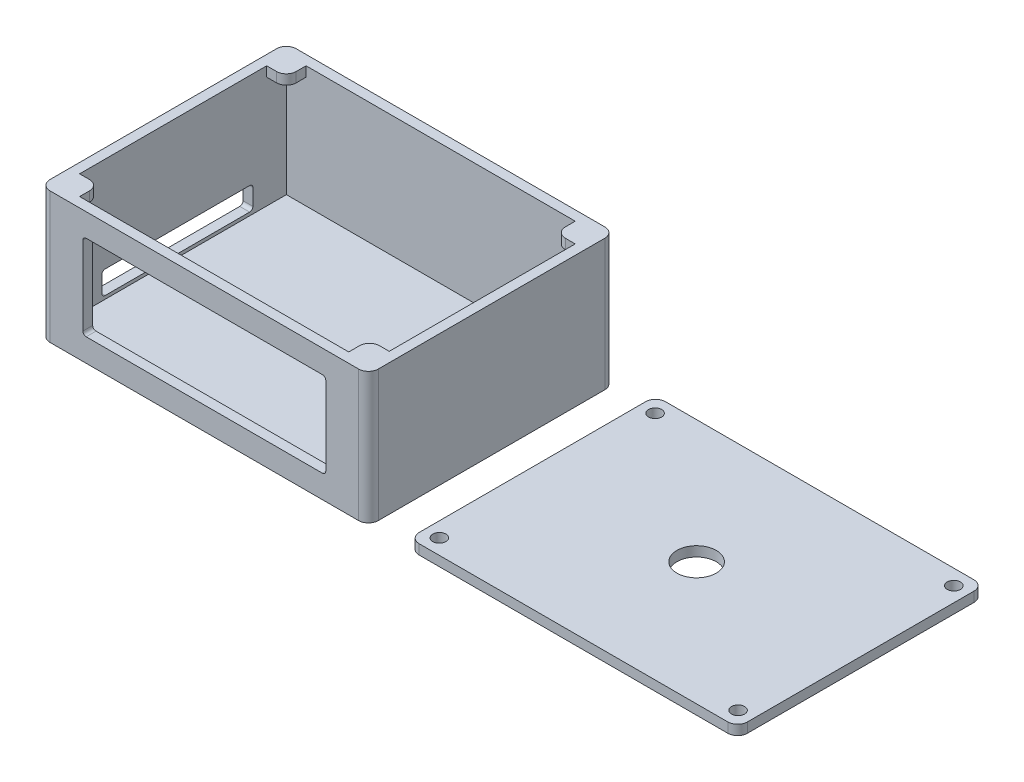
SolidWorks part; units mm, degrees
ref_plane "Ön Düzlem" through (0, 0, 0) normal (0, 0, 1) x (1, 0, 0)
ref_plane "Üst Düzlem" through (0, 0, 0) normal (0, 1, 0) x (1, 0, 0)
ref_plane "Sağ Düzlem" through (0, 0, 0) normal (1, 0, 0) x (0, 0, -1)
sketch "Çizim2" plane through (0, 0, 0) normal (0, 1, 0) x (1, 0, 0)
  line L1 (-45.5172, 36.2069) -> (54.4828, 36.2069)
  line L2 (-45.5172, 36.2069) -> (-45.5172, -38.7931)
  line L3 (-45.5172, -38.7931) -> (54.4828, -38.7931)
  line L4 (54.4828, 36.2069) -> (54.4828, -38.7931)
  dimension "D1" = 100
  dimension "D2" = 75
extrude "Yükseklik-Ekstrüzyon1" add sketch "Çizim2" along normal blind 40
sketch "Çizim4" plane through (0, 40, 0) normal (0, 1, 0) x (1, 0, 0)
  line L0 (4.4828, 36.2069) -> (4.4828, 33.2069)
  line L1 (54.4828, 36.2069) -> (-45.5172, 36.2069) construction
  line L2 (4.4828, -38.7931) -> (4.4828, -35.7931)
  line L3 (-45.5172, -38.7931) -> (54.4828, -38.7931) construction
  line L4 (54.4828, -1.2931) -> (51.4828, -1.2931)
  line L5 (54.4828, -38.7931) -> (54.4828, 36.2069) construction
  line L6 (-45.5172, -1.2931) -> (-42.5172, -1.2931)
  line L7 (-45.5172, 36.2069) -> (-45.5172, -38.7931) construction
  line L9 (-42.5172, -35.7931) -> (51.4828, -35.7931)
  line L10 (51.4828, -35.7931) -> (51.4828, 33.2069)
  line L11 (51.4828, 33.2069) -> (-42.5172, 33.2069)
  line L12 (-42.5172, 33.2069) -> (-42.5172, -35.7931)
extrude "Kes-Ekstrüzyon1" cut sketch "Çizim4" against normal blind 37 contours L12 L9 L10 L11
sketch "Çizim6" plane through (0, 0, 0) normal (0, 0, 1) x (1, 0, 0)
  line L0 (4.4828, 40) -> (4.4828, 0)
  line L1 (-45.5172, 40) -> (54.4828, 40) construction
  line L2 (-45.5172, 0) -> (54.4828, 0) construction
  line L3 (-45.5172, 20) -> (54.4828, 20)
  line L4 (-45.5172, 40) -> (-45.5172, 0) construction
  line L5 (54.4828, 40) -> (54.4828, 0) construction
  line L6 (4.4828, 20) -> (4.4828, 7)
  line L8 (41.4828, 7) -> (41.4828, 33)
  line L9 (41.4828, 33) -> (-32.5172, 33)
  line L10 (-32.5172, 33) -> (-32.5172, 7)
  line L11 (-32.5172, 7) -> (41.4828, 7)
  dimension "D1" = 74
  dimension "D2" = 26
extrude "Kes-Ekstrüzyon2" cut sketch "Çizim6" along normal blind 218 contours L11 L8 L9 L10
sketch "Çizim7" plane through (-45.5172, 0, 0) normal (-1, 0, 0) x (0, 0, 1)
  line L0 (0, 0) -> (0, 4)
  line L2 (23, 4) -> (23, 11)
  line L3 (23, 11) -> (-23, 11)
  line L4 (-23, 11) -> (-23, 4)
  line L5 (-23, 4) -> (23, 4)
extrude "Kes-Ekstrüzyon3" cut sketch "Çizim7" against normal blind 30 contours L4 L5 L2 L3
fillet "Radyus1" radius 3 4 edges at (-45.5172, 20, -36.2069) (54.4828, 20, -36.2069) (54.4828, 20, 38.7931) (-45.5172, 20, 38.7931)
sketch "Çizim9" plane through (0, 40, 0) normal (0, 1, 0) x (1, 0, 0)
  line L0 (-42.5172, 33.2069) -> (-36.5172, 33.2069)
  line L2 (51.4828, 33.2069) -> (-42.5172, 33.2069) construction
  line L3 (-36.5172, 33.2069) -> (-36.5172, 27.2069)
  line L4 (-36.5172, 27.2069) -> (-42.5172, 27.2069)
  line L5 (-42.5172, 33.2069) -> (-42.5172, -35.7931) construction
  line L6 (-42.5172, 27.2069) -> (-42.5172, 33.2069)
extrude "Yükseklik-Ekstrüzyon2" add sketch "Çizim9" against normal blind 3
fillet "Radyus2" radius 3 1 edges at (-36.5172, 38.5, -27.2069)
sketch "Çizim11" plane through (0, 40, 0) normal (0, 1, 0) x (1, 0, 0)
  line L0 (51.4828, 33.2069) -> (45.4828, 33.2069)
  line L1 (51.4828, 33.2069) -> (-42.5172, 33.2069) construction
  line L2 (45.4828, 33.2069) -> (45.4828, 27.2069)
  line L3 (45.4828, 27.2069) -> (51.4828, 27.2069)
  line L4 (51.4828, -35.7931) -> (51.4828, 33.2069) construction
  line L5 (51.4828, 27.2069) -> (51.4828, 33.2069)
extrude "Yükseklik-Ekstrüzyon3" add sketch "Çizim11" against normal blind 3
fillet "Radyus3" radius 3 1 edges at (45.4828, 38.5, -27.2069)
sketch "Çizim12" plane through (0, 40, 0) normal (0, 1, 0) x (1, 0, 0)
  line L0 (-42.5172, -35.7931) -> (-42.5172, -29.7931)
  line L1 (-42.5172, 27.2069) -> (-42.5172, -35.7931) construction
  line L2 (-42.5172, -29.7931) -> (-36.5172, -29.7931)
  line L3 (-36.5172, -29.7931) -> (-36.5172, -35.7931)
  line L4 (-42.5172, -35.7931) -> (51.4828, -35.7931) construction
  line L5 (-36.5172, -35.7931) -> (-42.5172, -35.7931)
extrude "Yükseklik-Ekstrüzyon4" add sketch "Çizim12" against normal blind 3
sketch "Çizim13" plane through (0, 40, 0) normal (0, 1, 0) x (1, 0, 0)
  line L0 (51.4828, -35.7931) -> (51.4828, -29.4609)
  line L1 (51.4828, -35.7931) -> (51.4828, 27.2069) construction
  line L2 (51.4828, -29.4609) -> (45.4828, -29.4609)
  line L3 (45.4828, -29.4609) -> (45.4828, -35.7931)
  line L4 (-36.5172, -35.7931) -> (51.4828, -35.7931) construction
  line L5 (45.4828, -35.7931) -> (51.4828, -35.7931)
extrude "Yükseklik-Ekstrüzyon5" add sketch "Çizim13" against normal blind 3
fillet "Radyus4" radius 3 2 edges at (-36.5172, 38.5, 29.7931) (45.4828, 38.5, 29.4609)
fillet "Radyus5" radius 1 4 edges at (-44.0172, 4, 23) (-44.0172, 11, 23) (-44.0172, 4, -23) (-44.0172, 11, -23)
fillet "Radyus7" radius 1 4 edges at (-32.5172, 33, 37.2931) (41.4828, 33, 37.2931) (41.4828, 7, 37.2931) (-32.5172, 7, 37.2931)
sketch "Çizim15" plane through (0, 0, 0) normal (0, -1, 0) x (1, 0, 0)
  line L1 (66.8296, 35.6644) -> (66.8296, -36.3356)
  line L2 (66.8296, -36.3356) -> (166.8296, -36.3356)
  line L3 (166.8296, -36.3356) -> (166.8296, 38.6644)
  line L4 (166.8296, 38.6644) -> (66.8296, 38.6644)
  line L5 (66.8296, 38.6644) -> (66.8296, 35.6644)
extrude "Yükseklik-Ekstrüzyon6" add sketch "Çizim15" against normal blind 3 separate body
fillet "Radyus10" radius 3 4 edges at (66.8296, 1.5, -36.3356) (66.8296, 1.5, 38.6644) (166.8296, 1.5, -36.3356) (166.8296, 1.5, 38.6644)
sketch "Çizim16" plane through (0, 3, 0) normal (0, 1, 0) x (1, 0, 0)
  circle A0 centre (116.8296, -1.1644) radius 6
extrude "Kes-Ekstrüzyon4" cut sketch "Çizim16" against normal blind 34 and the other way blind 31
sketch "Çizim17" plane through (0, 3, 0) normal (0, 1, 0) x (1, 0, 0)
  line L0 (51.4828, 27.2069) -> (51.4828, 36.2069)
  line L1 (45.4828, 33.2069) -> (54.4828, 33.2069)
  line L2 (51.4828, 31.7069) -> (45.4828, 31.7069)
  line L3 (49.9828, 33.2069) -> (49.9828, 31.7069)
  line L4 (49.9828, 31.7069) -> (74.509, 31.7069)
  line L5 (66.8296, 31.7069) -> (71.3296, 31.7069)
  line L6 (66.8296, -35.6644) -> (66.8296, 33.3356) construction
  line L7 (71.3296, 31.7069) -> (71.3296, 36.3356)
  line L8 (69.8296, 36.3356) -> (163.8296, 36.3356) construction
  line L9 (116.8296, 36.3356) -> (116.8296, -38.6644)
  line L10 (163.8296, -38.6644) -> (69.8296, -38.6644) construction
  line L11 (66.8296, -1.1644) -> (166.8296, -1.1644)
  line L12 (166.8296, 33.3356) -> (166.8296, -35.6644) construction
  circle A0 centre (71.3296, 31.7069) radius 2
  circle A1 centre (162.3296, 31.7069) radius 2
  circle A2 centre (162.3296, -34.0357) radius 2
  circle A3 centre (71.3296, -34.0357) radius 2
extrude "Kes-Ekstrüzyon5" cut sketch "Çizim17" against normal blind 20 contours A2 | A3 | A0 | A1
sketch "Çizim18" plane through (0, 0, 0) normal (0, 1, 0) x (1, 0, 0)
